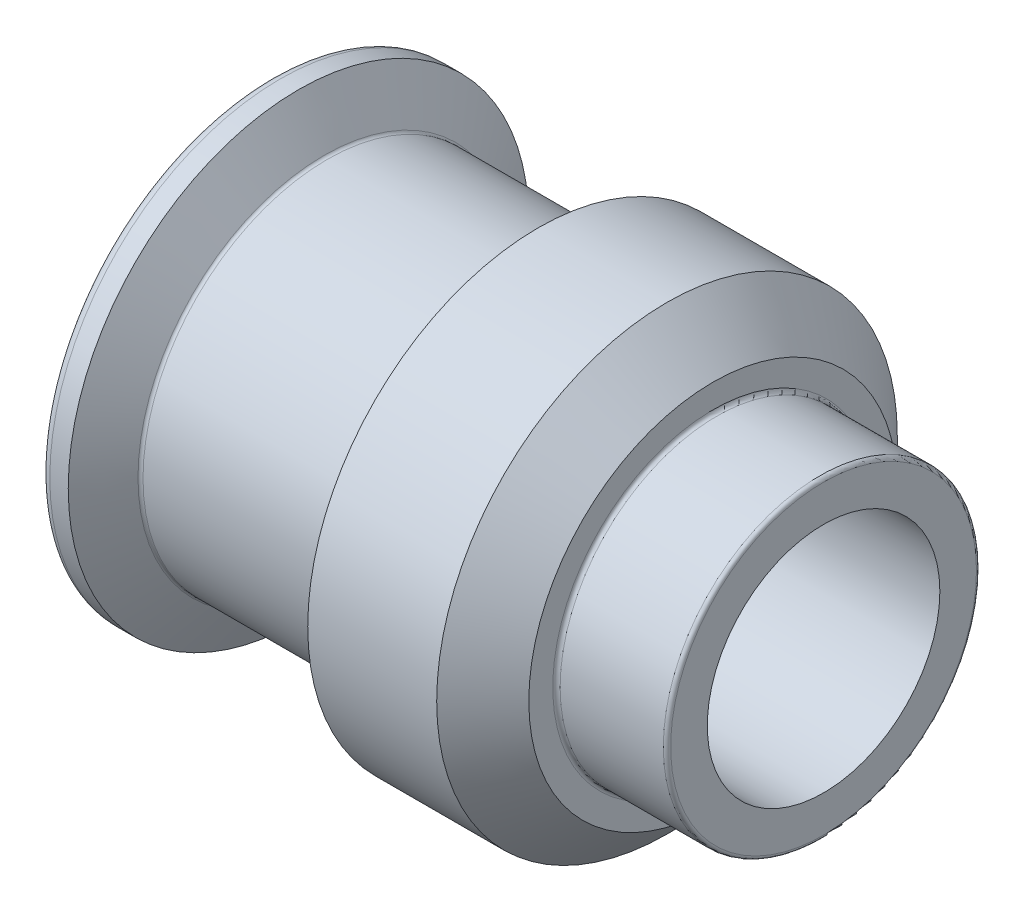
SolidWorks part; units mm, degrees
ref_plane "Plane1" through (0, 0, 0) normal (0, 0, 1) x (1, 0, 0)
ref_plane "Plane2" through (0, 0, 0) normal (0, 1, 0) x (1, 0, 0)
ref_plane "Plane3" through (0, 0, 0) normal (1, 0, 0) x (0, 0, -1)
sketch "Sketch1" plane through (0, 0, 0) normal (0, 0, 1) x (1, 0, 0)
  line L0 (0, 12.625) -> (0, 16.6)
  line L1 (-0.4, 17) -> (-11.6, 17)
  line L2 (-60, 24) -> (-60, 7)
  line L3 (-17, 25) -> (-12, 20)
  line L5 (-12, 17.4) -> (-12, 20)
  line L6 (-17, 25) -> (-31, 25)
  line L7 (-31, 25) -> (-33.7713, 20.2)
  line L8 (-34.1177, 20) -> (-53.8823, 20)
  line L9 (-54.2287, 20.2) -> (-57, 25)
  line L10 (-57, 25) -> (-59, 25)
  line L11 (-27, 12.625) -> (-30.2476, 7)
  line L12 (-27, 12.625) -> (0, 12.625)
  line L13 (0, 0) -> (-50, 0) construction
  line L14 (-30.2476, 7) -> (-60, 7)
  arc A0 (-59, 25) -> (-60, 24) centre (-59, 24) ccw
  arc A1 (-11.6, 17) -> (-12, 17.4) centre (-11.6, 17.4) cw
  arc A3 (-0.4, 17) -> (0, 16.6) centre (-0.4, 16.6) cw
  arc A4 (-33.7713, 20.2) -> (-34.1177, 20) centre (-34.1177, 20.4) cw
  arc A5 (-53.8823, 20) -> (-54.2287, 20.2) centre (-53.8823, 20.4) cw
  dimension "D5" = 1
  dimension "D11" = 0.4
  dimension "D19" = 0.4
  dimension "D3" = 34
  dimension "D4" = 25.25
  dimension "D6" = 60
  dimension "D7" = 27
  dimension "D8" = 60
  dimension "D9" = 12
  dimension "D10" = 50
  dimension "D12" = 14
  dimension "D13" = 40
  dimension "D14" = 60
  dimension "D15" = 60
  dimension "D16" = 19
  dimension "D17" = 3
  dimension "D20" = 5
  dimension "D21" = 45
revolve "Base-Revolve" add sketch "Sketch1" angle 360 about L13
cosmetic thread "Cosmetic Thread1" parameters "D2"=16
